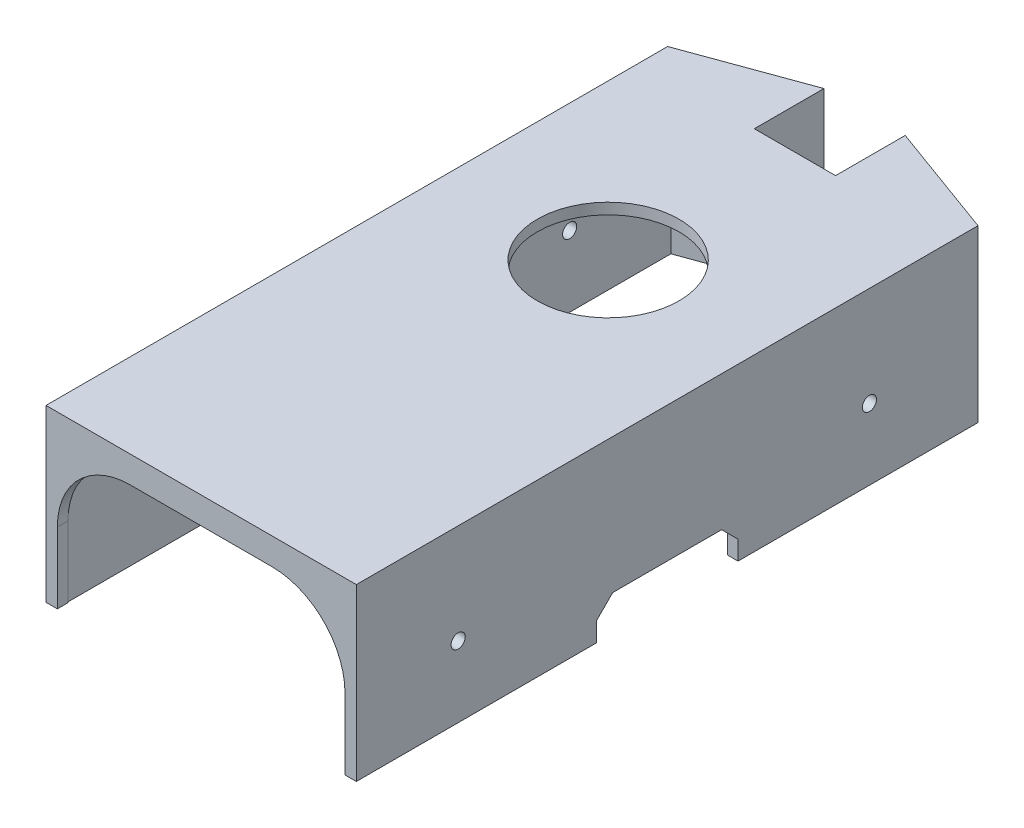
SolidWorks part; units mm, degrees
ref_plane "Front Plane" through (0, 0, 0) normal (0, 0, 1) x (1, 0, 0)
ref_plane "Top Plane" through (0, 0, 0) normal (0, 1, 0) x (1, 0, 0)
ref_plane "Right Plane" through (0, 0, 0) normal (1, 0, 0) x (0, 0, -1)
sketch "Sketch1" plane through (0, 0, 0) normal (0, 1, 0) x (1, 0, 0)
  line L8 (-21.4352, -43.5768) -> (19.3648, -43.5768)
  line L9 (19.3648, -43.5768) -> (19.3648, 41.611)
  line L10 (19.3648, 41.611) -> (6.1982, 46.4104)
  line L11 (6.1982, 46.4104) -> (6.1982, 37.2232)
  line L12 (6.1982, 37.2232) -> (-8.2687, 37.2232)
  line L13 (-8.2687, 37.2232) -> (-8.2687, 46.4104)
  line L14 (-8.2687, 46.4104) -> (-21.4352, 41.611)
  line L15 (-21.4352, 41.611) -> (-21.4352, -43.5768)
  line L16 (-22.9352, -45.0768) -> (20.8648, -45.0768)
  line L17 (20.8648, -45.0768) -> (20.8648, 42.6607)
  line L18 (20.8648, 42.6607) -> (4.6982, 48.5537)
  line L19 (4.6982, 48.5537) -> (4.6982, 38.7232)
  line L20 (4.6982, 38.7232) -> (-6.7687, 38.7232)
  line L21 (-6.7687, 38.7232) -> (-6.7687, 48.5537)
  line L22 (-6.7687, 48.5537) -> (-22.9352, 42.6607)
  line L23 (-22.9352, 42.6607) -> (-22.9352, -45.0768)
  dimension "D1" = 1.5
extrude "Boss-Extrude1" add sketch "Sketch1" along normal blind 50
sketch "Sketch2" plane through (0, 50, 0) normal (0, 1, 0) x (1, 0, 0)
  line L8 (-22.9352, 42.6607) -> (-22.9352, -45.0768)
  line L9 (-22.9352, -45.0768) -> (20.8648, -45.0768)
  line L10 (20.8648, -45.0768) -> (20.8648, 42.6607)
  line L11 (20.8648, 42.6607) -> (4.6982, 48.5537)
  line L12 (4.6982, 48.5537) -> (4.6982, 38.7232)
  line L13 (4.6982, 38.7232) -> (-6.7687, 38.7232)
  line L14 (-6.7687, 38.7232) -> (-6.7687, 48.5537)
  line L15 (-6.7687, 48.5537) -> (-22.9352, 42.6607)
  line L16 (-22.9352, 42.6607) -> (-22.9352, -45.0768)
  line L17 (-22.9352, -45.0768) -> (20.8648, -45.0768)
  line L18 (20.8648, -45.0768) -> (20.8648, 42.6607)
  line L19 (20.8648, 42.6607) -> (4.6982, 48.5537)
  line L20 (4.6982, 48.5537) -> (4.6982, 38.7232)
  line L21 (4.6982, 38.7232) -> (-6.7687, 38.7232)
  line L22 (-6.7687, 38.7232) -> (-6.7687, 48.5537)
  line L23 (-6.7687, 48.5537) -> (-22.9352, 42.6607)
  dimension "D1" = 0
extrude "Boss-Extrude2" add sketch "Sketch2" along normal blind 1.52
sketch "Sketch3" plane through (0, 0, 45.0768) normal (0, 0, 1) x (1, 0, 0)
  line L1 (-21.0352, 10) -> (-21.0352, 0)
  line L2 (-21.0352, 0) -> (18.9648, 0)
  line L3 (18.9648, 0) -> (18.9648, 10)
  line L4 (-22.9352, 0) -> (20.8648, 0) construction
  line L5 (8.9648, 20.3) -> (-11.0352, 20.3)
  line L6 (-21.3352, 10) -> (-21.3352, -0.3)
  line L7 (-21.3352, -0.3) -> (19.2648, -0.3)
  line L8 (19.2648, -0.3) -> (19.2648, 10)
  line L9 (8.9648, 20) -> (-11.0352, 20) construction
  arc A0 (18.9648, 10) -> (8.9648, 20) centre (8.9648, 10) ccw
  arc A1 (-11.0352, 20) -> (-21.0352, 10) centre (-11.0352, 10) ccw
  arc A4 (-11.0352, 20.3) -> (-21.3352, 10) centre (-11.0352, 10) ccw
  arc A5 (19.2648, 10) -> (8.9648, 20.3) centre (8.9648, 10) ccw
  point P12 (-1.0352, 0)
  point P13 (-1.0352, 0)
  line M1 (-22.9352, 0) -> (20.8648, 0)
  dimension "D1" = 0.3
extrude "Cut-Extrude2" cut sketch "Sketch3" against normal blind 1.52 contours A0 L9 A1 L1 L3 M1 | L9 A0 L3 L8 A5 L5 A4 L6 L1 A1 M1
sketch "Sketch4" plane through (0, 51.52, 0) normal (0, 1, 0) x (1, 0, 0)
  line L8 (-6.7687, 48.5537) -> (-22.9352, 42.6607)
  line L9 (-22.9352, 42.6607) -> (-22.9352, -45.0768)
  line L10 (-22.9352, -45.0768) -> (20.8648, -45.0768)
  line L11 (20.8648, -45.0768) -> (20.8648, 42.6607)
  line L12 (20.8648, 42.6607) -> (4.6982, 48.5537)
  line L13 (4.6982, 48.5537) -> (4.6982, 38.7232)
  line L14 (4.6982, 38.7232) -> (-6.7687, 38.7232)
  line L15 (-6.7687, 38.7232) -> (-6.7687, 48.5537)
  line L16 (-6.7687, 48.5537) -> (-22.9352, 42.6607)
  line L17 (-22.9352, 42.6607) -> (-22.9352, -45.0768)
  line L18 (-22.9352, -45.0768) -> (20.8648, -45.0768)
  line L19 (20.8648, -45.0768) -> (20.8648, 42.6607)
  line L20 (20.8648, 42.6607) -> (4.6982, 48.5537)
  line L21 (4.6982, 48.5537) -> (4.6982, 38.7232)
  line L22 (4.6982, 38.7232) -> (-6.7687, 38.7232)
  line L23 (-6.7687, 38.7232) -> (-6.7687, 48.5537)
  dimension "D1" = 0
extrude "Cut-Extrude3" cut sketch "Sketch4" against normal blind 29
sketch "Sketch5" plane through (0, 22.52, 0) normal (0, 1, 0) x (1, 0, 0)
  line L8 (-6.7687, 38.7232) -> (-6.7687, 48.5537)
  line L9 (-6.7687, 48.5537) -> (-22.9352, 42.6607)
  line L10 (-22.9352, 42.6607) -> (-22.9352, -45.0768)
  line L11 (-22.9352, -45.0768) -> (20.8648, -45.0768)
  line L12 (20.8648, -45.0768) -> (20.8648, 42.6607)
  line L13 (20.8648, 42.6607) -> (4.6982, 48.5537)
  line L14 (4.6982, 48.5537) -> (4.6982, 38.7232)
  line L15 (4.6982, 38.7232) -> (-6.7687, 38.7232)
  line L16 (-6.7687, 38.7232) -> (-6.7687, 48.5537)
  line L17 (-6.7687, 48.5537) -> (-22.9352, 42.6607)
  line L18 (-22.9352, 42.6607) -> (-22.9352, -45.0768)
  line L19 (-22.9352, -45.0768) -> (20.8648, -45.0768)
  line L20 (20.8648, -45.0768) -> (20.8648, 42.6607)
  line L21 (20.8648, 42.6607) -> (4.6982, 48.5537)
  line L22 (4.6982, 48.5537) -> (4.6982, 38.7232)
  line L23 (4.6982, 38.7232) -> (-6.7687, 38.7232)
  dimension "D1" = 0
extrude "Boss-Extrude3" add sketch "Sketch5" along normal blind 1.55
sketch "Sketch6" plane through (20.8648, 0, 0) normal (1, 0, 0) x (0, 0, -1)
  line L0 (-46.847, 10) -> (-46.847, 0)
  line L2 (42.6607, 0) -> (42.6607, 5)
  line L4 (-41.847, 5) -> (-41.847, 10)
  line L5 (-41.847, 10) -> (-46.847, 10)
  circle A0 centre (-29.2802, 10) radius 1
  circle A1 centre (28.753, 10) radius 1
extrude "Cut-Extrude4" cut sketch "Sketch6" against normal blind 77.55 contours A1 | A0
sketch "Sketch7" plane through (20.8648, 0, 0) normal (1, 0, 0) x (0, 0, -1)
  line L0 (-8.8919, 5) -> (-11.208, 2.6838)
  line L1 (-11.208, 2.6838) -> (-11.208, 0)
  line L2 (8.792, 2.6838) -> (8.792, 0)
  line L3 (6.4758, 5) -> (8.792, 2.6838)
  line L4 (42.6607, 0) -> (42.6607, 24.07)
  line L5 (42.6607, 24.07) -> (-45.0768, 24.07)
  line L6 (-45.0768, 24.07) -> (-45.0768, 0)
  line L7 (-45.0768, 0) -> (42.6607, 0)
  line L8 (42.6607, 0) -> (42.6607, 24.07)
  line L9 (42.6607, 24.07) -> (-45.0768, 24.07)
  line L10 (-45.0768, 24.07) -> (-45.0768, 0)
  line L11 (-45.0768, 0) -> (42.6607, 0)
  line L12 (-8.8919, 5) -> (6.4758, 5)
  line L13 (-11.208, 0) -> (8.792, 0)
  point P2 (-1.208, 0)
  point P11 (-1.208, 0)
  line M10 (-45.0768, 0) -> (42.6607, 0)
  dimension "D1" = 0
extrude "Cut-Extrude5" cut sketch "Sketch7" against normal blind 77.55 contours L12 L0 L1 L2 L3 M10
sketch "Sketch8" plane through (20.8648, 0, 0) normal (1, 0, 0) x (0, 0, -1)
  line L0 (-29.2802, 10) -> (28.753, 10) construction
  line L1 (8.792, 2.6838) -> (8.792, 0)
  line L2 (8.792, 0) -> (42.6607, 0)
  line L3 (42.6607, 0) -> (42.6607, 51.52)
  line L4 (42.6607, 51.52) -> (-45.0768, 51.52)
  line L5 (-45.0768, 51.52) -> (-45.0768, 0)
  line L6 (-45.0768, 0) -> (-11.208, 0)
  line L7 (-11.208, 0) -> (-11.208, 2.6838)
  line L8 (-11.208, 2.6838) -> (-8.8919, 5)
  line L9 (-8.8919, 5) -> (6.4758, 5)
  line L10 (6.4758, 5) -> (8.792, 2.6838)
  line L21 (8.792, 2.6838) -> (8.792, 0)
  line L22 (8.792, 0) -> (42.6607, 0)
  line L23 (42.6607, 0) -> (42.6607, 24.07)
  line L24 (42.6607, 24.07) -> (-45.0768, 24.07)
  line L25 (-45.0768, 24.07) -> (-45.0768, 0)
  line L26 (-45.0768, 0) -> (-11.208, 0)
  line L27 (-11.208, 0) -> (-11.208, 2.6838)
  line L28 (-11.208, 2.6838) -> (-8.8919, 5)
  line L29 (-8.8919, 5) -> (6.4758, 5)
  line L30 (6.4758, 5) -> (8.792, 2.6838)
  line L31 (8.792, 2.6838) -> (8.792, 0)
  line L32 (8.792, 0) -> (42.6607, 0)
  line L33 (42.6607, 0) -> (42.6607, 24.07)
  line L34 (42.6607, 24.07) -> (-45.0768, 24.07)
  line L35 (-45.0768, 24.07) -> (-45.0768, 0)
  line L36 (-45.0768, 0) -> (-11.208, 0)
  line L37 (-11.208, 0) -> (-11.208, 2.6838)
  line L38 (-11.208, 2.6838) -> (-8.8919, 5)
  line L39 (-8.8919, 5) -> (6.4758, 5)
  line L40 (6.4758, 5) -> (8.792, 2.6838)
  circle A0 centre (-30.7036, 10) radius 1
  circle A1 centre (27.3296, 10) radius 1
  circle M11 centre (-29.2802, 10) radius 1
  circle M12 centre (28.753, 10) radius 1
  dimension "D1" = 0
extrude "Cut-Extrude6" cut sketch "Sketch8" against normal blind 70 contours L0 A1 M12 | A1 L0 M12 | A0 M11
sketch "Sketch10" plane through (20.8648, 0, 0) normal (1, 0, 0) x (0, 0, -1)
  circle A0 centre (27.3296, 10) radius 1
  arc A1 (28.0413, 9.2975) -> (28.0413, 10.7025) centre (28.753, 10) ccw construction
  arc A2 (28.0413, 9.2975) -> (28.0413, 10.7025) centre (28.753, 10) ccw
  arc A3 (-29.9919, 10.7025) -> (-29.9919, 9.2975) centre (-30.7036, 10) ccw construction
  arc A4 (-29.9919, 10.7025) -> (-29.9919, 9.2975) centre (-30.7036, 10) ccw
  circle A5 centre (-30.7036, 10) radius 1
  arc A6 (-29.9919, 9.2975) -> (-29.9919, 10.7025) centre (-29.2802, 10) ccw construction
  arc A7 (-29.9919, 9.2975) -> (-29.9919, 10.7025) centre (-29.2802, 10) ccw
  arc M1 (-29.9919, 10.7025) -> (-29.9919, 9.2975) centre (-29.2802, 10) cw
  arc M3 (28.0413, 10.7025) -> (28.0413, 9.2975) centre (28.753, 10) cw
extrude "Boss-Extrude4" add sketch "Sketch10" against normal up to surface (1.5 mm away) contours A5 M1 | A0 M3 up to face at (19.3648, 10, -28.0413)
sketch "Sketch11" plane through (-22.9352, 0, 0) normal (-1, 0, 0) x (0, 0, 1)
  line L10 (-41.611, 0) -> (-8.792, 0)
  line L11 (-8.792, 0) -> (-8.792, 2.6838)
  line L12 (-8.792, 2.6838) -> (-6.4758, 5)
  line L13 (-6.4758, 5) -> (8.8919, 5)
  line L14 (8.8919, 5) -> (11.208, 2.6838)
  line L15 (11.208, 2.6838) -> (11.208, 0)
  line L16 (11.208, 0) -> (43.5768, 0)
  line L17 (43.5768, 0) -> (43.5768, 22.52)
  line L18 (43.5768, 22.52) -> (-41.611, 22.52)
  line L19 (-41.611, 22.52) -> (-41.611, 0)
  line L20 (-41.611, 0) -> (-8.792, 0)
  line L21 (-8.792, 0) -> (-8.792, 2.6838)
  line L22 (-8.792, 2.6838) -> (-6.4758, 5)
  line L23 (-6.4758, 5) -> (8.8919, 5)
  line L24 (8.8919, 5) -> (11.208, 2.6838)
  line L25 (11.208, 2.6838) -> (11.208, 0)
  line L26 (11.208, 0) -> (43.5768, 0)
  line L27 (43.5768, 0) -> (43.5768, 22.52)
  line L28 (43.5768, 22.52) -> (-41.611, 22.52)
  line L29 (-41.611, 22.52) -> (-41.611, 0)
  circle A0 centre (30.7036, 10) radius 1 construction
  arc A1 (29.9919, 9.2975) -> (29.9919, 10.7025) centre (30.7036, 10) ccw construction
  circle A2 centre (-27.3296, 10) radius 1 construction
  circle A3 centre (30.7036, 10) radius 1
  arc A4 (29.9919, 9.2975) -> (29.9919, 10.7025) centre (30.7036, 10) ccw
  circle A5 centre (-27.3296, 10) radius 1
  arc M11 (29.9919, 9.2975) -> (29.9919, 10.7025) centre (29.2802, 10) cw
  arc M12 (29.9919, 10.7025) -> (29.9919, 9.2975) centre (30.7036, 10) cw
  arc M13 (-28.0413, 9.2975) -> (-28.0413, 10.7025) centre (-28.753, 10) cw
  arc M14 (-28.0413, 10.7025) -> (-28.0413, 9.2975) centre (-27.3296, 10) cw
  line M15 (-8.792, 0) -> (-8.792, 2.6838)
  line M16 (-8.792, 2.6838) -> (-6.4758, 5)
  line M17 (-6.4758, 5) -> (8.8919, 5)
  line M18 (8.8919, 5) -> (11.208, 2.6838)
  line M19 (11.208, 2.6838) -> (11.208, 0)
  line M20 (11.208, 0) -> (45.0768, 0)
  line M24 (-42.6607, 0) -> (-8.792, 0)
  dimension "D1" = 0
extrude "Boss-Extrude5" add sketch "Sketch11" against normal up to surface (1.5 mm away) contours A5 M13 | A3 M11 | L28 L29 L27 M24 M15 M16 M17 M18 M19 M20 M14 M13 M12 M11 up to face at (-21.4352, 10, -28.0413)
sketch "Sketch12" plane through (0, 24.07, 0) normal (0, 1, 0) x (1, 0, 0)
  line L0 (-1.0352, 38.7232) -> (-1.0352, 12.3632) construction
  line L1 (4.6982, 38.7232) -> (-6.7687, 38.7232) construction
  circle A0 centre (-1.0352, 12.3632) radius 10
  dimension "D2" = 20
  dimension "D1" = 26.36
extrude "Cut-Extrude7" cut sketch "Sketch12" against normal blind 70
